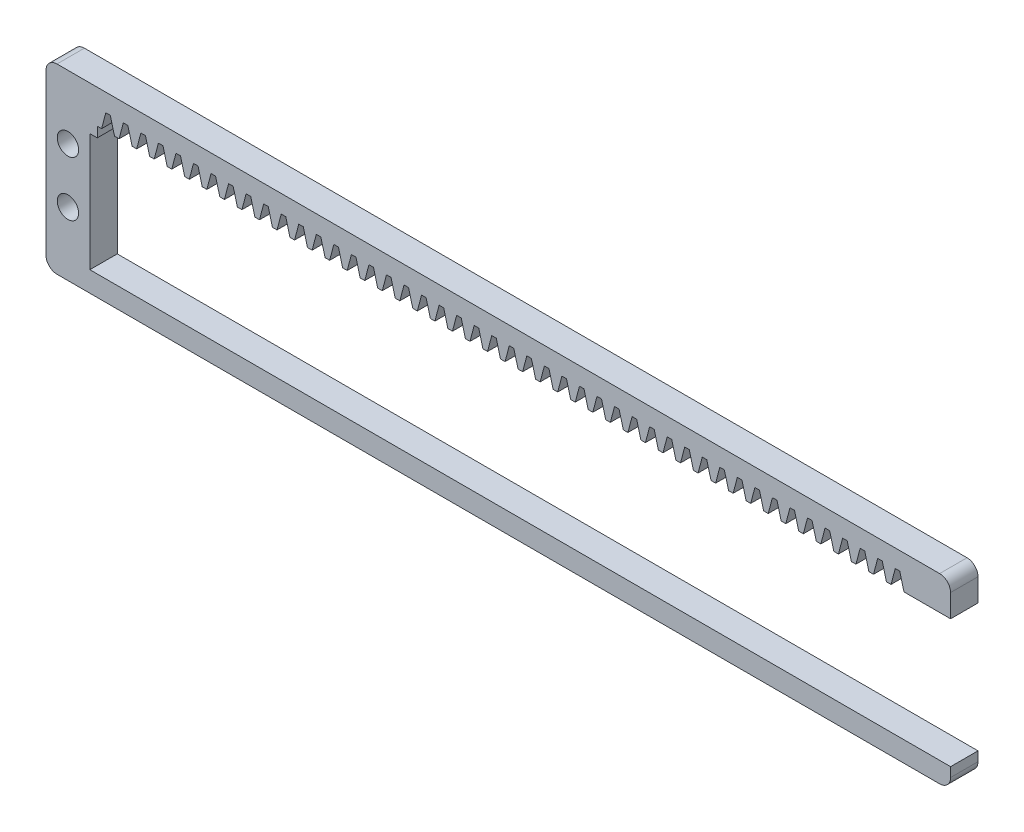
SolidWorks part; units mm, degrees
other "Markup1"
sketch "Sketch6" plane through (0, -30, 3.6) normal (0, 0, 1) x (1, 0, 0)
other "Markup2"
sketch "Sketch7" plane through (0, -30, 3.6) normal (0, 0, 1) x (1, 0, 0)
ref_plane "Front Plane" through (0, 0, 0) normal (0, 0, 1) x (1, 0, 0)
ref_plane "Top Plane" through (0, 0, 0) normal (0, 1, 0) x (1, 0, 0)
ref_plane "Right Plane" through (0, 0, 0) normal (1, 0, 0) x (0, 0, -1)
sketch "Sketch1" plane through (0, 0, 0) normal (0, 0, 1) x (1, 0, 0)
  line L1 (2, 0) -> (163, 0)
  line L2 (0, -2) -> (0, -31.22)
  line L3 (2, -33.22) -> (163, -33.22)
  line L4 (165, -2) -> (165, -31.22)
  arc A0 (163, -33.22) -> (165, -31.22) centre (163, -31.22) ccw
  arc A1 (0, -31.22) -> (2, -33.22) centre (2, -31.22) ccw
  arc A2 (2, 0) -> (0, -2) centre (2, -2) ccw
  arc A3 (163, 0) -> (165, -2) centre (163, -2) cw
  point P7 (165, -33.22)
  point P12 (0, 0)
  point P15 (165, 0)
  dimension "D3" = 2
  dimension "D1" = 33.22
  dimension "D2" = 165
extrude "Boss-Extrude1" add sketch "Sketch1" along normal blind 5
sketch "Sketch2" plane through (0, 0, 5) normal (0, 0, 1) x (1, 0, 0)
  line L0 (2, -33.22) -> (163, -33.22) construction
  line L1 (8, -8) -> (157, -8)
  line L2 (8, -8) -> (8, -29.5)
  line L3 (8, -29.5) -> (157, -29.5)
  line L4 (157, -8) -> (157, -29.5)
  line L5 (0, -2) -> (0, -31.22) construction
  line L7 (165, -31.22) -> (165, -2) construction
  line L8 (8, -18.75) -> (157, -18.75) construction
  line L12 (8, -29.5) -> (157, -29.5) construction
  line L13 (157, -4.3144) -> (157, -29.5) construction
  dimension "D1" = 21.5
  dimension "D2" = 8
  dimension "D3" = 8
  dimension "D4" = 3.72
extrude "Cut-Extrude1" cut sketch "Sketch2" against normal through all
sketch "Sketch3" plane through (0, 0, 5) normal (0, 0, 1) x (1, 0, 0)
  line L0 (157, -8) -> (8, -8) construction
  line L1 (9.35, -8) -> (155.32, -8)
  line L2 (9.35, -8) -> (9.35, -6.15)
  line L3 (9.35, -6.15) -> (155.32, -6.15)
  line L4 (155.32, -8) -> (155.32, -6.15)
  line L5 (157, -29.5) -> (157, -8) construction
  line L6 (8, -8) -> (8, -29.5) construction
  dimension "D1" = 1.85
  dimension "D2" = 1.68
  dimension "D3" = 1.35
extrude "Cut-Extrude2" cut sketch "Sketch3" against normal through all
sketch "Sketch4" plane through (0, 0, 5) normal (0, 0, 1) x (1, 0, 0)
  line L0 (157.7, -6.15) -> (156.5, -6.15) construction
  line L1 (155.32, -6.15) -> (9.35, -6.15) construction
  line L2 (157.7, -6.15) -> (158.465, -3.2492) construction
  line L3 (158.465, -3.2492) -> (155.735, -3.2492) construction
  line L4 (155.735, -3.2492) -> (156.5, -6.15)
  line L5 (155.735, -3.2492) -> (154.905, -3.2492)
  line L6 (154.905, -3.2492) -> (154.14, -6.15)
  line L7 (154.14, -6.15) -> (156.5, -6.15)
  line L10 (156.5, -6.15) -> (157.7, -6.15) construction
  dimension "D1" = 1.2
  dimension "D3" = 3
  dimension "D4" = 0.83
  dimension "D5" = 2.73
extrude "Cut-Extrude4" cut sketch "Sketch4" against normal through all
pattern_linear "LPattern1" count 46 spacing 3.2 along (-1, 0, 0) of "Cut-Extrude4"
sketch "Sketch5" plane through (0, 0, 5) normal (0, 0, 1) x (1, 0, 0)
  line L0 (157, -16.61) -> (165, -16.61) construction
  line L1 (163, 0) -> (2, 0) construction
  line L2 (8, -8) -> (8, -29.5) construction
  line L3 (0, -2) -> (0, -31.22) construction
  line L4 (2, -33.22) -> (163, -33.22) construction
  line L5 (0, -16.61) -> (8, -16.61) construction
  line L7 (161, -11.61) -> (161, -21.61) construction
  line L8 (4, -11.61) -> (4, -21.61) construction
  line L9 (157, -29.5) -> (157, -8) construction
  line L10 (165, -31.22) -> (165, -2) construction
  circle A4 centre (4, -11.61) radius 1.95
  circle A5 centre (4, -21.61) radius 1.95
  circle A6 centre (161, -11.61) radius 1.95
  circle A7 centre (161, -21.61) radius 1.95
  point P8 (161, -16.61)
  point P31 (161, -16.61)
  dimension "D1" = 3.9
  dimension "D2" = 4
  dimension "D3" = 3.9
  dimension "D4" = 3.9
  dimension "D6" = 3.9
  dimension "D5" = 10
  dimension "D7" = 10
extrude "Cut-Extrude5" cut sketch "Sketch5" against normal blind 10
sketch "Sketch8" plane through (0, -29.5, 0) normal (0, 1, 0) x (1, 0, 0)
  line L0 (165, 0) -> (165, -5)
  line L1 (165, 0) -> (152.5086, 0)
  line L2 (165, -5) -> (152.5086, -5)
  line L3 (152.5086, 0) -> (152.5086, -5)
extrude "Cut-Extrude6" cut sketch "Sketch8" along normal up to surface (23.35 mm away) up to face at (153.72, -6.15, 2.5)
